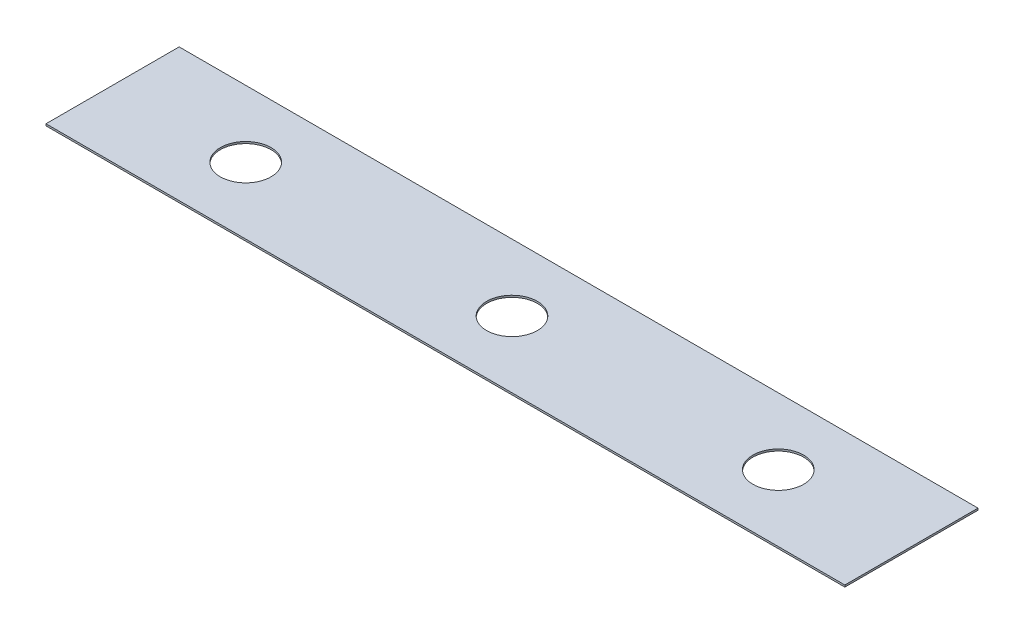
SolidWorks part; units mm, degrees
ref_plane "Front Plane" through (0, 0, 0) normal (0, 0, 1) x (1, 0, 0)
ref_plane "Top Plane" through (0, 0, 0) normal (0, 1, 0) x (1, 0, 0)
ref_plane "Right Plane" through (0, 0, 0) normal (1, 0, 0) x (0, 0, -1)
sketch "Sketch1" plane through (0, 0, 0) normal (0, 1, 0) x (1, 0, 0)
  line L1 (-38.1, 6.35) -> (38.1, 6.35)
  line L2 (-38.1, 6.35) -> (-38.1, -6.35)
  line L3 (-38.1, -6.35) -> (38.1, -6.35)
  line L4 (38.1, 6.35) -> (38.1, -6.35)
  line L5 (-38.1, 6.35) -> (38.1, -6.35) construction
  line L6 (-38.1, -6.35) -> (38.1, 6.35) construction
  point P0 (0, 0)
  dimension "D1" = 12.7
  dimension "D2" = 76.2
extrude "Boss-Extrude1" add sketch "Sketch1" along normal blind 0.1778
sketch "Sketch2" plane through (0, 0.1778, 0) normal (0, 1, 0) x (1, 0, 0)
  circle A0 centre (0, 0) radius 2.4194
  circle A1 centre (-25.4, 0) radius 2.4193
  circle A2 centre (25.4, 0) radius 2.4193
  dimension "D3" = 4.8387
  dimension "D1" = 25.4
  dimension "D2" = 25.4
extrude "Cut-Extrude1" cut sketch "Sketch2" against normal through all
